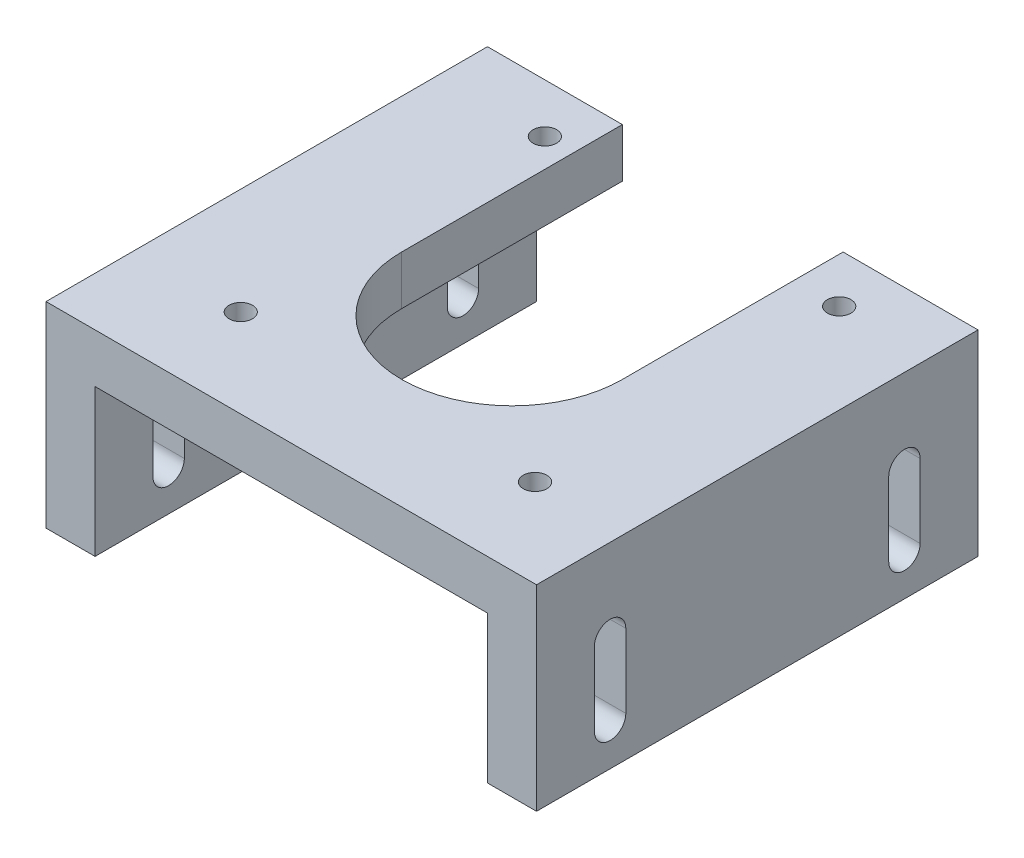
SolidWorks part; units mm, degrees
ref_plane "Front Plane" through (0, 0, 0) normal (0, 0, 1) x (1, 0, 0)
ref_plane "Top Plane" through (0, 0, 0) normal (0, 1, 0) x (1, 0, 0)
ref_plane "Right Plane" through (0, 0, 0) normal (1, 0, 0) x (0, 0, -1)
sketch "Sketch1" plane through (0, 0, 0) normal (0, 0, 1) x (1, 0, 0)
  line L1 (-25, 0) -> (-20, 0)
  line L2 (-20, 15) -> (20, 15)
  line L3 (-20, 15) -> (-20, 0)
  line L5 (20, 15) -> (20, 0)
  line L6 (20, 0) -> (25, 0)
  line L10 (25, 0) -> (25, 20)
  line L11 (25, 20) -> (-25, 20)
  line L14 (-25, 0) -> (-25, 20)
  point P0 (0, 0)
  point P1 (0, 20)
  point P3 (0, 15)
  point P10 (0, 0)
  point P11 (0, 0)
  point P13 (0, 0)
  point P14 (0, 0)
  dimension "D1" = 40
  dimension "D2" = 5
  dimension "D3" = 15
  dimension "D4" = 5
  dimension "D6" = 5
extrude "Boss-Extrude1" add sketch "Sketch1" along normal blind 45
sketch "Sketch2" plane through (0, 20, 0) normal (0, 1, 0) x (1, 0, 0)
  line L0 (0, 0) -> (0, -25.7902) construction
  line L1 (25, 0) -> (-25, 0) construction
  line L2 (11.25, 0) -> (11.25, -22.5)
  line L3 (-11.25, 0) -> (-11.25, -22.5)
  line L4 (25, -45) -> (25, 0) construction
  line L6 (-11.25, 0) -> (11.25, 0)
  arc A0 (11.25, -22.5) -> (-11.25, -22.5) centre (0, -22.5) cw
  point P11 (25, -22.5)
  dimension "D1" = 22.5
extrude "Cut-Extrude1" cut sketch "Sketch2" against normal up to next
sketch "Sketch3" plane through (0, 20, 0) normal (0, 1, 0) x (1, 0, 0)
  line L0 (25, 0) -> (11.25, 0) construction
  line L3 (25, -45) -> (25, 0) construction
  circle A0 centre (15.85, -36) radius 1.2
  circle A1 centre (-14.15, -36) radius 1.2
  circle A2 centre (-14.15, -5) radius 1.2
  circle A3 centre (15.85, -5) radius 1.2
  dimension "D1" = 2.4
  dimension "D2" = 31
  dimension "D3" = 5
  dimension "D4" = 30
  dimension "D5" = 9.15
extrude "Cut-Extrude2" cut sketch "Sketch3" against normal blind 10
sketch "Sketch4" plane through (25, 0, 0) normal (1, 0, 0) x (0, 0, -1)
  line L0 (-37.5, 11.6) -> (-37.5, 4.1) construction
  line L1 (-35.9, 11.6) -> (-35.9, 4.1)
  line L2 (-39.1, 11.6) -> (-39.1, 4.1)
  line L3 (-45, 0) -> (0, 0) construction
  line L5 (-22.5, 20) -> (-22.5, 0) construction
  line L6 (-45, 20) -> (0, 20) construction
  line L7 (-7.5, 11.6) -> (-7.5, 4.1) construction
  line L8 (-9.1, 11.6) -> (-9.1, 4.1)
  line L9 (-5.9, 11.6) -> (-5.9, 4.1)
  arc A0 (-35.9, 11.6) -> (-39.1, 11.6) centre (-37.5, 11.6) ccw
  arc A1 (-39.1, 4.1) -> (-35.9, 4.1) centre (-37.5, 4.1) ccw
  arc A2 (-9.1, 11.6) -> (-5.9, 11.6) centre (-7.5, 11.6) cw
  arc A3 (-5.9, 4.1) -> (-9.1, 4.1) centre (-7.5, 4.1) cw
  point P2 (-37.5, 7.85)
  point P9 (-37.5, 2.5)
  point P18 (-7.5, 7.85)
  dimension "D1" = 3.2
  dimension "D2" = 7.5
  dimension "D3" = 2.5
  dimension "D4" = 15
extrude "Cut-Extrude3" cut sketch "Sketch4" against normal through all both and the other way through all
